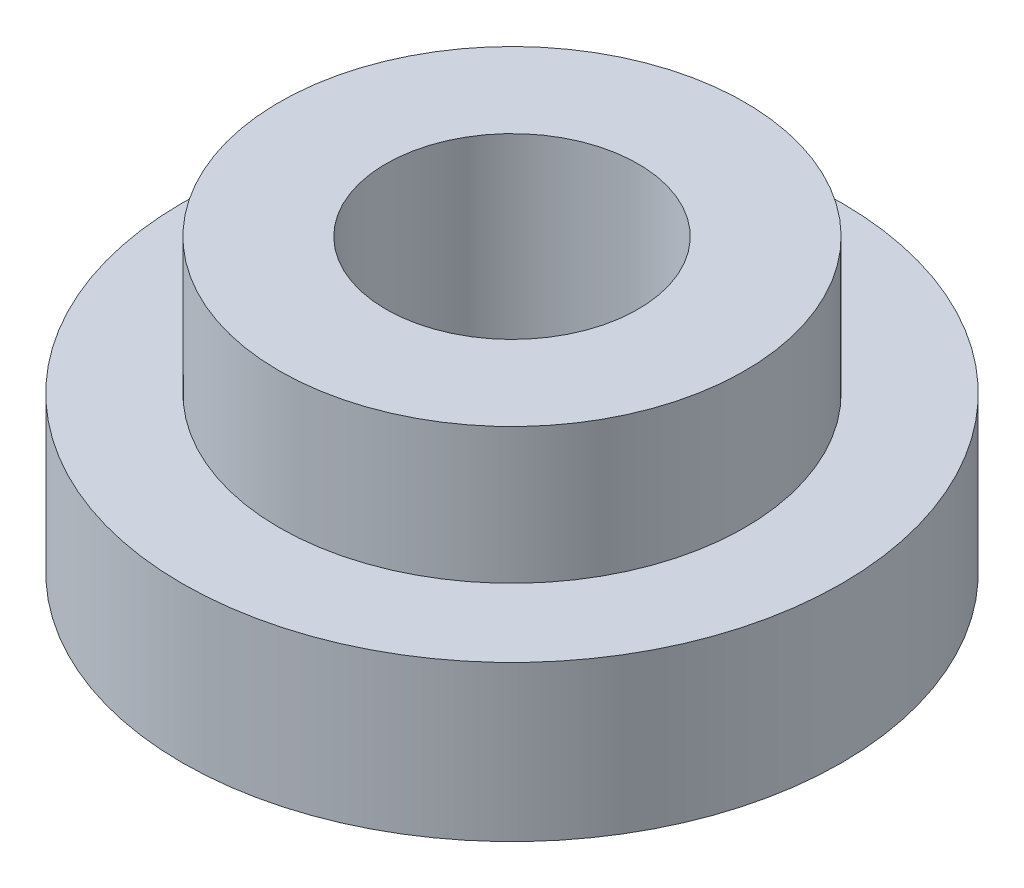
SolidWorks part; units mm, degrees
ref_plane "Front Plane" through (0, 0, 0) normal (0, 0, 1) x (1, 0, 0)
ref_plane "Top Plane" through (0, 0, 0) normal (0, 1, 0) x (1, 0, 0)
ref_plane "Right Plane" through (0, 0, 0) normal (1, 0, 0) x (0, 0, -1)
sketch "Sketch1" plane through (0, 0, 0) normal (0, 1, 0) x (1, 0, 0)
  circle A0 centre (0, 0) radius 4.318
extrude "Boss-Extrude1" add sketch "Sketch1" along normal blind 2.032
sketch "Sketch2" plane through (0, 2.032, 0) normal (0, 1, 0) x (1, 0, 0)
  circle A0 centre (0, 0) radius 3.048
extrude "Boss-Extrude2" add sketch "Sketch2" along normal blind 1.778
sketch "Sketch3" plane through (0, 3.81, 0) normal (0, 1, 0) x (1, 0, 0)
  circle A0 centre (0, 0) radius 1.651
extrude "Cut-Extrude1" cut sketch "Sketch3" against normal through all
